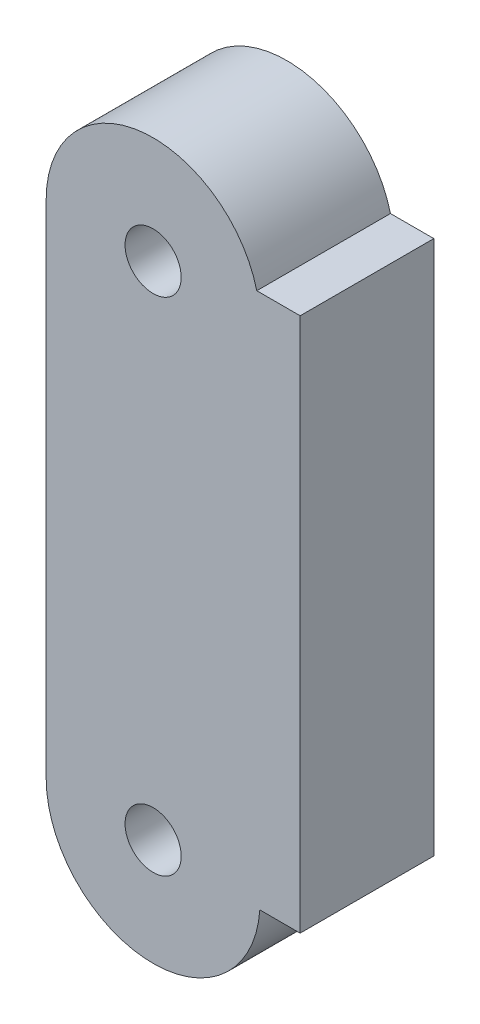
SolidWorks part; units mm, degrees
ref_plane "Alzado" through (0, 0, 0) normal (0, 0, 1) x (1, 0, 0)
ref_plane "Planta" through (0, 0, 0) normal (0, 1, 0) x (1, 0, 0)
ref_plane "Vista lateral" through (0, 0, 0) normal (1, 0, 0) x (0, 0, -1)
sketch "Croquis1" plane through (0, 0, 0) normal (0, 0, 1) x (1, 0, 0)
  line L4 (-3.2443, 35) -> (0, 35)
  line L5 (0, 35) -> (0, -5)
  line L6 (-3.0181, -5) -> (0, -5)
  line L7 (-19, 33.038) -> (-19, -4.462)
  arc A4 (-19, -4.462) -> (-3.0181, -5) centre (-11, -4.462) ccw
  circle A5 centre (-11, -4.462) radius 2.1
  arc A7 (-3.2443, 35) -> (-19, 33.038) centre (-11, 33.038) ccw
  circle A8 centre (-11, 33.038) radius 2.1
  point P2 (0, -4.462)
  point P3 (0, 0)
  point P6 (0, 0)
  point P10 (0, 0)
  point P12 (0, 0)
  point P13 (0.6969, 35)
  point P19 (-10.4216, 33.038)
  dimension "D2" = 4.2
  dimension "D1" = 37.5
extrude "Saliente-Extruir1" add sketch "Croquis1" along normal blind 10
